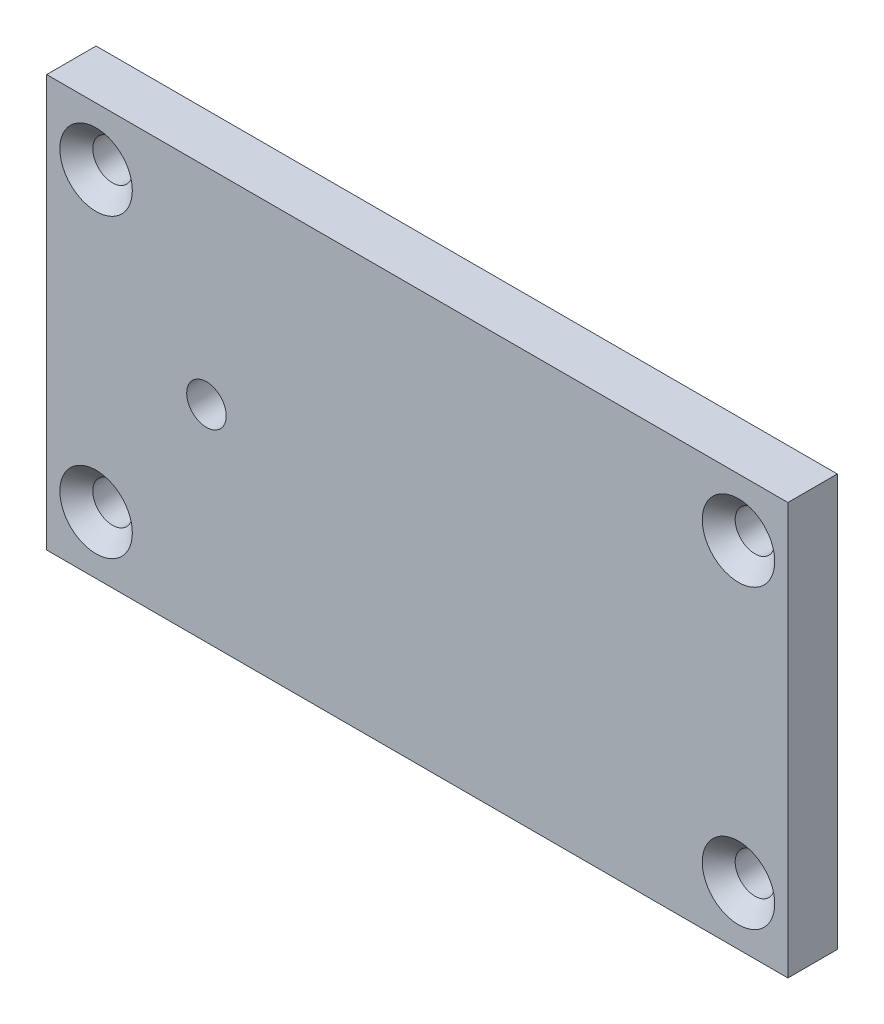
SolidWorks part; units mm, degrees
ref_plane "Front Plane" through (0, 0, 0) normal (0, 0, 1) x (1, 0, 0)
ref_plane "Top Plane" through (0, 0, 0) normal (0, 1, 0) x (1, 0, 0)
ref_plane "Right Plane" through (0, 0, 0) normal (1, 0, 0) x (0, 0, -1)
sketch "Sketch1" plane through (0, 0, 0) normal (0, 0, 1) x (1, 0, 0)
  line L1 (22.5, -12.5) -> (-22.5, -12.5)
  line L2 (22.5, -12.5) -> (22.5, 12.5)
  line L3 (22.5, 12.5) -> (-22.5, 12.5)
  line L4 (-22.5, -12.5) -> (-22.5, 12.5)
  line L5 (22.5, -12.5) -> (-22.5, 12.5) construction
  line L6 (22.5, 12.5) -> (-22.5, -12.5) construction
  point P0 (0, 0)
  dimension "D1" = 45
  dimension "D2" = 25
extrude "Boss-Extrude1" add sketch "Sketch1" along normal blind 3
hole_wizard "CSK for M2 Flat Head Machine Screw1" positions "Sketch3" profile "Sketch2" countersink size "M2" standard "ANSI Metric" end condition through all
sketch "Sketch3" plane through (0, 0, 3) normal (0, 0, 1) x (1, 0, 0)
  line L0 (-19.5, 10.2544) -> (-19.5, 9) construction
  line L1 (-19.5, 9) -> (19.5, 9) construction
  line L2 (19.5, 9) -> (19.5, -9) construction
  line L3 (19.5, -9) -> (-19.5, -9) construction
  line L4 (-19.5, -9) -> (-19.5, 9) construction
  point P0 (-19.5, 9)
  point P2 (19.5, 9)
  point P4 (19.5, -9)
  point P6 (-19.5, -9)
  dimension "D1" = 39
  dimension "D2" = 18
  dimension "D3" = 9
  dimension "D4" = 19.5
sketch "Sketch2" plane through (-19.5, 9, 3) normal (1, 0, 0) x (0, -1, 0)
  line L0 (0, 0) -> (0, 3)
  line L1 (0, 3) -> (1.2, 3)
  line L2 (1.2, 3) -> (1.2, 1)
  line L3 (1.2, 1) -> (2.2, 0)
  line L5 (2.2, 0) -> (0, 0)
  line L6 (-1.2, 1) -> (-2.2, 0) construction
  line L11 (0, -6.35) -> (0, 107.95) construction
  dimension "Thru Hole Dia." = 2.4
  dimension "Thru Hole Depth" = 3
  dimension "Near C'Sink Dia." = 4.4
  dimension "Near C'Sink Angle" = 90
hole_wizard "CSK for M2 Flat Head Machine Screw2" positions "Sketch5" profile "Sketch4" countersink size "M2" standard "ANSI Metric" end condition through all
sketch "Sketch5" plane through (0, 0, 0) normal (0, 0, -1) x (-1, 0, 0)
  line L0 (22.5, 12.5) -> (22.5, -12.5) construction
  point P0 (12.8, 0)
  dimension "D1" = 9.7
sketch "Sketch4" plane through (-12.8, 0, 0) normal (1, 0, 0) x (0, 1, 0)
  line L0 (0, 0) -> (0, 3)
  line L1 (0, 3) -> (1.2, 3)
  line L2 (1.2, 3) -> (1.2, 1)
  line L3 (1.2, 1) -> (2.2, 0)
  line L5 (2.2, 0) -> (0, 0)
  line L6 (-1.2, 1) -> (-2.2, 0) construction
  line L11 (0, -6.35) -> (0, 107.95) construction
  dimension "Thru Hole Dia." = 2.4
  dimension "Thru Hole Depth" = 3
  dimension "Near C'Sink Dia." = 4.4
  dimension "Near C'Sink Angle" = 90
